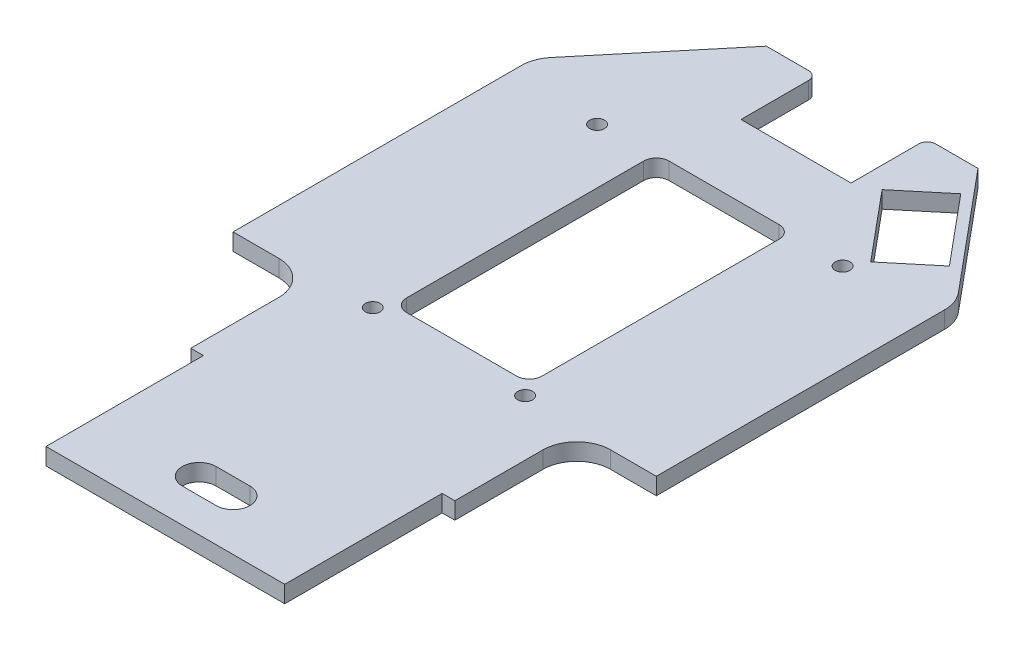
SolidWorks part; units mm, degrees
ref_plane "Front Plane" through (0, 0, 0) normal (0, 0, 1) x (1, 0, 0)
ref_plane "Top Plane" through (0, 0, 0) normal (0, 1, 0) x (1, 0, 0)
ref_plane "Right Plane" through (0, 0, 0) normal (1, 0, 0) x (0, 0, -1)
sketch "Sketch1" plane through (0, 0, 0) normal (0, 1, 0) x (1, 0, 0)
  line L0 (-28.2, -67) -> (28.2, -67)
  line L1 (31.2, -29.8) -> (31.2, -9)
  line L2 (39.2, -1) -> (50, -1)
  line L3 (50, -1) -> (50, 67.1036)
  line L4 (48.1458, 72.2251) -> (25, 100)
  line L5 (25, 100) -> (25, 82) construction
  line L6 (13, 82) -> (-13, 82)
  line L7 (-25, 82) -> (-25, 100) construction
  line L8 (-25, 100) -> (-48.1458, 72.2251)
  line L9 (-50, 67.1036) -> (-50, -1)
  line L10 (-50, -1) -> (-39.2, -1)
  line L11 (-31.2, -9) -> (-31.2, -29.8)
  line L12 (0, -301.7456) -> (0, 401.93) construction
  line L13 (-50, 70) -> (50, 70) construction
  line L14 (126.3715, 0) -> (-162.7022, 0) construction
  line L15 (132.1823, 64) -> (-95.3575, 64) construction
  line L16 (-13, 3) -> (13, 3)
  line L17 (-16, 6) -> (-16, 62)
  line L18 (-13, 65) -> (13, 65)
  line L19 (16, 6) -> (16, 62)
  line L20 (-16, 3) -> (16, 65) construction
  line L21 (-16, 65) -> (16, 3) construction
  line L22 (-4, -55) -> (4, -55) construction
  line L23 (-4, -51) -> (4, -51)
  line L24 (-4, -59) -> (4, -59)
  line L25 (-25, 100) -> (-15, 100)
  line L26 (-13, 98) -> (-13, 82)
  line L27 (25, 100) -> (15, 100)
  line L28 (13, 98) -> (13, 82)
  line L29 (-13, 82) -> (-25, 82) construction
  line L30 (25, 82) -> (13, 82) construction
  line L31 (31.2, -29.8) -> (28.2, -29.8)
  line L32 (28.2, -29.8) -> (28.2, -67)
  line L33 (-31.2, -29.8) -> (-28.2, -29.8)
  line L34 (-28.2, -29.8) -> (-28.2, -67)
  line L35 (-31.2, -29.8) -> (-31.2, -67) construction
  line L36 (-31.2, -67) -> (-28.2, -67) construction
  line L37 (28.2, -67) -> (31.2, -67) construction
  line L38 (31.2, -67) -> (31.2, -29.8) construction
  line L39 (28.1609, 92.7705) -> (41.6047, 76.6378)
  line L40 (41.6047, 76.6378) -> (31.4642, 68.1874)
  line L41 (31.4642, 68.1874) -> (18.0203, 84.32)
  line L42 (18.0203, 84.32) -> (28.1609, 92.7705)
  line L43 (36.5729, 86.1125) -> (22.9166, 74.7323) construction
  circle A0 centre (18, 0) radius 1.75
  circle A1 centre (-18, 0) radius 1.75
  circle A2 centre (29, 64) radius 1.75
  circle A3 centre (-29, 64) radius 1.75
  arc A4 (-13, 3) -> (-16, 6) centre (-13, 6) cw
  arc A5 (13, 3) -> (16, 6) centre (13, 6) ccw
  arc A6 (13, 65) -> (16, 62) centre (13, 62) cw
  arc A7 (-16, 62) -> (-13, 65) centre (-13, 62) cw
  arc A8 (50, 67.1036) -> (48.1458, 72.2251) centre (42, 67.1036) ccw
  arc A9 (-48.1458, 72.2251) -> (-50, 67.1036) centre (-42, 67.1036) ccw
  arc A10 (31.2, -9) -> (39.2, -1) centre (39.2, -9) cw
  arc A11 (-39.2, -1) -> (-31.2, -9) centre (-39.2, -9) cw
  arc A12 (-4, -51) -> (-4, -59) centre (-4, -55) ccw
  arc A13 (4, -59) -> (4, -51) centre (4, -55) ccw
  arc A14 (15, 100) -> (13, 98) centre (15, 98) ccw
  arc A15 (-15, 100) -> (-13, 98) centre (-15, 98) cw
  point P15 (0, 34)
  point P32 (0, -55)
  point P54 (31.2, -1)
  dimension "D13" = 18
  dimension "D15" = 3.5
  dimension "D16" = 3
  dimension "D17" = 8
  dimension "D18" = 8
  dimension "D23" = 2
  dimension "D2" = 66
  dimension "D3" = 100
  dimension "D4" = 67
  dimension "D5" = 137
  dimension "D6" = 50
  dimension "D7" = 30
  dimension "D8" = 18
  dimension "D9" = 32
  dimension "D10" = 66
  dimension "D11" = 4
  dimension "D12" = 64
  dimension "D14" = 29
  dimension "D19" = 12
  dimension "D20" = 8
  dimension "D21" = 8
  dimension "D22" = 26
  dimension "D24" = 56.4
  dimension "D25" = 37.2
  dimension "D26" = 3
  dimension "D27" = 2.2
  dimension "D28" = 13.2
  dimension "D29" = 21
extrude "Boss-Extrude1" add sketch "Sketch1" along normal blind 4
